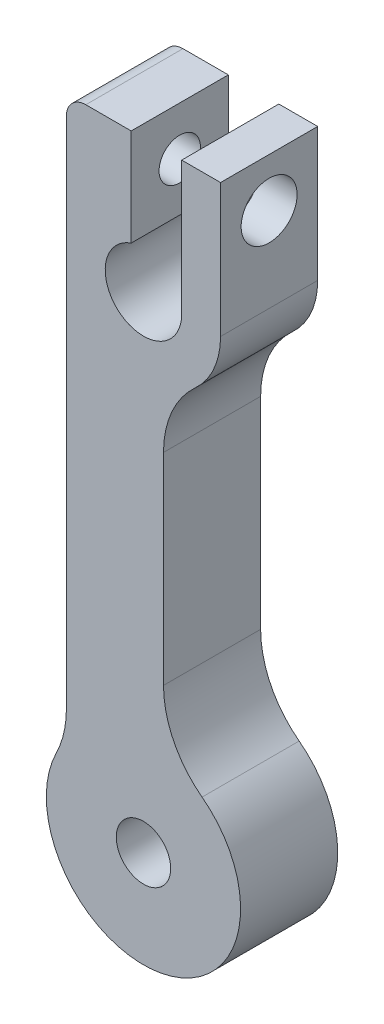
SolidWorks part; units mm, degrees
material "6061-T6 (SS)"
ref_plane "Front Plane" through (0, 0, 0) normal (0, 0, 1) x (1, 0, 0)
ref_plane "Top Plane" through (0, 0, 0) normal (0, 1, 0) x (1, 0, 0)
ref_plane "Right Plane" through (0, 0, 0) normal (1, 0, 0) x (0, 0, -1)
sketch "Sketch1" plane through (0, 0, 0) normal (0, 0, 1) x (1, 0, 0)
  line L0 (-5.04, 40.4679) -> (-5.04, 31.75)
  line L1 (-5.04, 31.75) -> (-5.04, 5.6176)
  line L2 (-0.802, 34.1179) -> (-0.802, 40.4679)
  line L3 (2.5, 31.75) -> (2.5, 40.4679)
  line L4 (2.5, 40.4679) -> (5.04, 40.4679)
  line L5 (1.31, 10.1299) -> (1.31, 23.3205)
  line L6 (-0.802, 40.4679) -> (-5.04, 40.4679)
  line L7 (0, 31.75) -> (0, 69.7149) construction
  line L9 (5.04, 31.75) -> (5.04, 40.4679)
  arc A0 (-5.04, 5.6176) -> (-5.695, 2.8088) centre (-11.39, 5.6176) cw
  arc A1 (-5.695, 2.8088) -> (3.83, 5.0649) centre (0, 0) ccw
  arc A2 (-0.802, 34.1179) -> (2.5, 31.75) centre (0, 31.75) ccw
  circle A3 centre (0, 0) radius 1.778
  arc A4 (1.31, 10.1299) -> (3.83, 5.0649) centre (7.66, 10.1299) ccw
  arc A5 (5.04, 31.75) -> (3.3895, 28.02) centre (0, 31.75) cw
  arc A6 (1.31, 23.3205) -> (3.3895, 28.02) centre (7.66, 23.3205) cw
  point P6 (0, 60.8184)
  dimension "D2" = 5
  dimension "D3" = 3.556
  dimension "D6" = 6.35
  dimension "D1" = 31.75
  dimension "D4" = 3.302
  dimension "D5" = 6.35
  dimension "D7" = 2.54
  dimension "D8" = 2.54
  dimension "D9" = 6.35
extrude "Boss-Extrude1" add sketch "Sketch1" along normal blind 6.35
fillet "Fillet1" radius 1.27 1 edges at (-5.04, 40.4679, 3.175)
hole_wizard "#6-32 Tapped Hole1" positions "Sketch3" profile "Sketch2" tap size "#6-32" standard "ANSI Inch" end condition through all
sketch "Sketch3" plane through (-5.04, 0, 0) normal (-1, 0, 0) x (0, 0, 1)
  line L0 (6.35, 39.1979) -> (6.35, 5.6176) construction
  line L1 (0, 40.4679) -> (6.35, 40.4679) construction
  point P0 (3.175, 37.2929)
  dimension "D1" = 3.175
  dimension "D2" = 3.175
sketch "Sketch2" plane through (-5.04, 37.2929, 3.175) normal (0, 1, 0) x (0, 0, 1)
  line L0 (0, 0) -> (0, 11.39)
  line L1 (0, 11.39) -> (1.3525, 11.39)
  line L2 (1.3525, 11.39) -> (1.3525, 0)
  line L5 (1.3525, 0) -> (0, 0)
  line L11 (0, -6.35) -> (0, 107.95) construction
  dimension "Thru Tap Drill Dia." = 2.7051
  dimension "Thru Tap Drill Depth" = 11.39
cosmetic thread "Hole Thread1" parameters "D2"=3.5052
hole_wizard "#6 Clearance Hole1" positions "3DSketch1" profile "Sketch5" hole size "#6" standard "ANSI Inch"
sketch3d "3DSketch1"
  circle A0 centre (5.04, 37.2929, 3.175) radius 1.3525 construction
  point P0 (5.04, 37.2929, 3.175)
  point P5 (3.6875, 37.2929, 3.175)
sketch "Sketch5" plane through (5.04, 37.2929, 3.175) normal (0, 1, 0) x (0, 0, -1)
  line L0 (0, 0) -> (0, 4.2739)
  line L1 (0, 4.2739) -> (1.8288, 3.175)
  line L2 (1.8288, 3.175) -> (1.8288, 0)
  line L5 (1.8288, 0) -> (0, 0)
  line L10 (0, 4.2739) -> (-1.8288, 3.175) construction
  line L11 (0, -6.35) -> (0, 107.95) construction
  dimension "Hole Dia." = 3.6576
  dimension "Hole Depth" = 3.175
  dimension "Drill Angle" = 118
